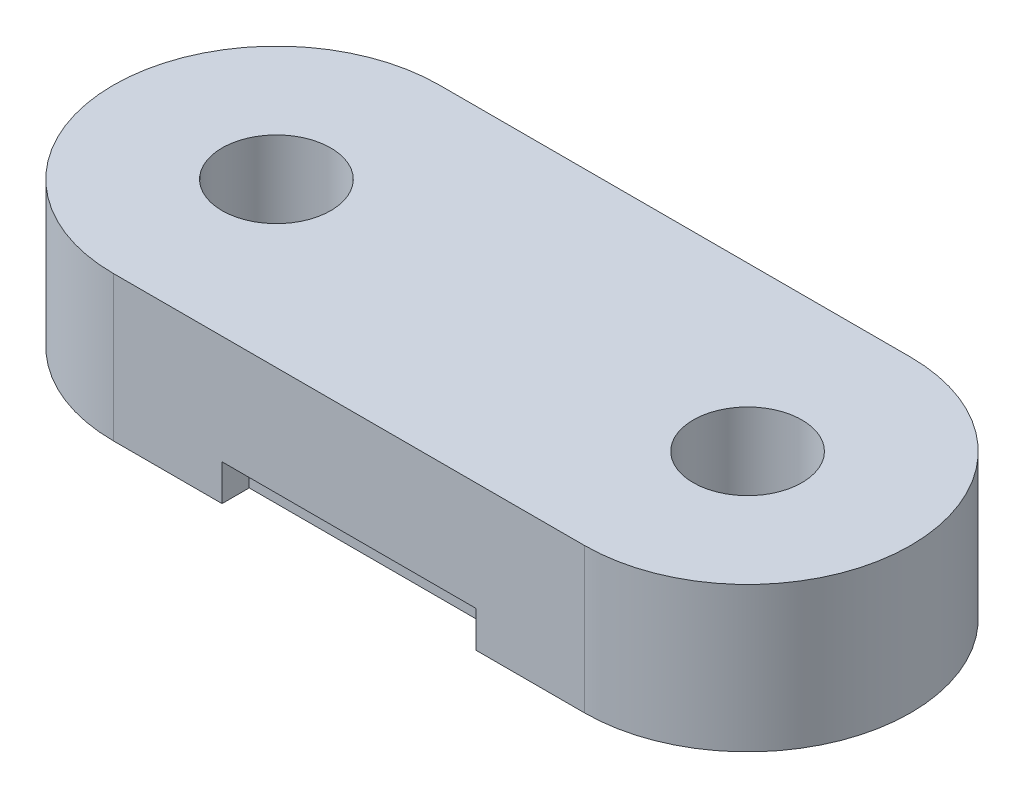
SolidWorks part; units mm, degrees
ref_plane "Front Plane" through (0, 0, 0) normal (0, 0, 1) x (1, 0, 0)
ref_plane "Top Plane" through (0, 0, 0) normal (0, 1, 0) x (1, 0, 0)
ref_plane "Right Plane" through (0, 0, 0) normal (1, 0, 0) x (0, 0, -1)
sketch "Sketch1" plane through (0, 0, 0) normal (0, 1, 0) x (1, 0, 0)
  line L0 (-6.5, 4.5) -> (6.5, 4.5)
  line L1 (-6.5, -4.5) -> (6.5, -4.5)
  circle A0 centre (6.5, 0) radius 1.5
  circle A1 centre (-6.5, 0) radius 1.5
  arc A2 (-6.5, 4.5) -> (-6.5, -4.5) centre (-6.5, 0) ccw
  arc A3 (6.5, -4.5) -> (6.5, 4.5) centre (6.5, 0) ccw
extrude "Extrude1" add sketch "Sketch1" along normal blind 4
sketch "Sketch2" plane through (0, 0, 0) normal (0, -1, 0) x (1, 0, 0)
  line L0 (-3.5, 4.5) -> (-3.5, -4.5)
  line L1 (-6.5, 4.5) -> (6.5, 4.5) construction
  line L2 (6.5, -4.5) -> (-6.5, -4.5) construction
  line L3 (3.5, 4.5) -> (3.5, -4.5)
  line L4 (-3.5, -0.75) -> (3.5, -0.75)
  line L5 (-3.5, 0.75) -> (3.5, 0.75)
  line L6 (-3.5, -2.25) -> (3.5, -2.25)
  line L7 (-3.5, -3.75) -> (3.5, -3.75)
  line L8 (-3.5, 3.75) -> (3.5, 3.75)
  line L9 (-3.5, 2.25) -> (3.5, 2.25)
  line L10 (-3.5, -4.5) -> (3.5, -4.5)
  line L11 (3.5, 4.5) -> (-3.5, 4.5)
  line M3 (-6.5, -4.5) -> (6.5, -4.5)
  line M5 (6.5, 4.5) -> (-6.5, 4.5)
extrude "Extrude4" cut sketch "Sketch2" against normal blind 1 contours L7 L0 L3 M3 | L0 L6 L3 L4 | L9 L0 L5 L3 | L0 L8 L3 M5
